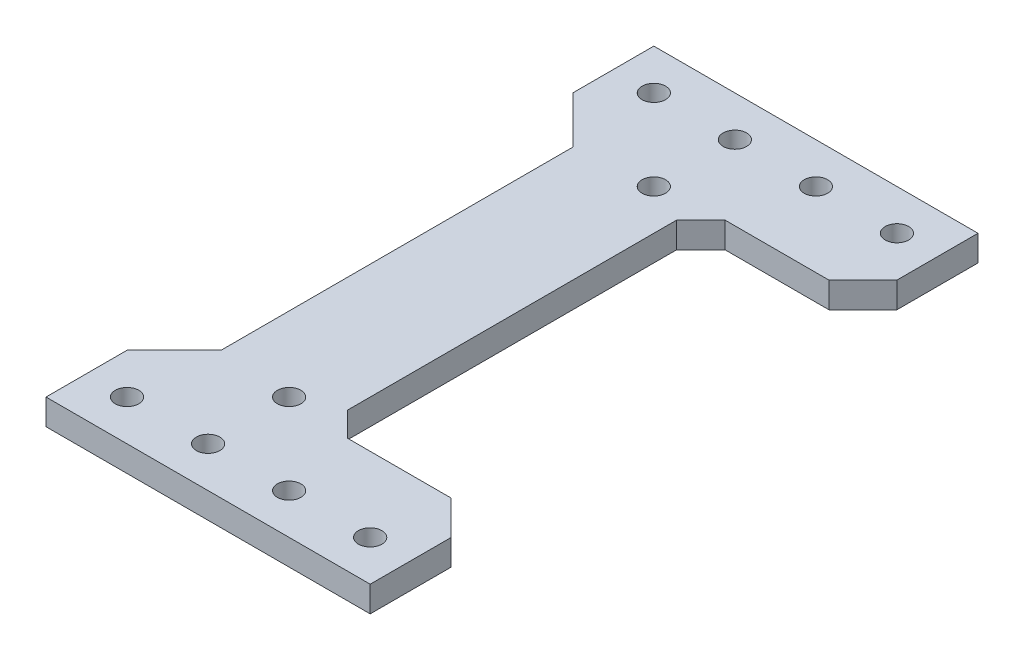
SolidWorks part; units mm, degrees
ref_plane "Front Plane" through (0, 0, 0) normal (0, 0, 1) x (1, 0, 0)
ref_plane "Top Plane" through (0, 0, 0) normal (0, 1, 0) x (1, 0, 0)
ref_plane "Right Plane" through (0, 0, 0) normal (1, 0, 0) x (0, 0, -1)
sketch "Sketch1" plane through (0, 0, 0) normal (0, 1, 0) x (1, 0, 0)
  line L0 (5, 23.3) -> (25, 23.3)
  line L1 (5, 0) -> (-9.2, 0)
  line L2 (5, 0) -> (5, 23.3)
  line L3 (-20, 32.5) -> (25, 32.5) construction
  line L4 (-9.2, 0) -> (-9.2, 21.7)
  line L5 (-15, 37.5) -> (25, 37.5)
  line L6 (-15, 37.5) -> (-15, 27.5)
  line L7 (-15, 27.5) -> (-9.2, 21.7)
  line L8 (25, 37.5) -> (25, 23.3)
  circle A0 centre (0, 22.5) radius 1.45
  circle A1 centre (-10, 32.5) radius 1.45
  circle A2 centre (20, 32.5) radius 1.45
  circle A3 centre (0, 32.5) radius 1.45
  circle A4 centre (10, 32.5) radius 1.45
  dimension "D4" = 2.9
  dimension "D1" = 37.5
  dimension "D2" = 10
  dimension "D3" = 14.2
  dimension "D5" = 20
  dimension "D6" = 10
  dimension "D7" = 5
  dimension "D8" = 10
  dimension "D9" = 5
  dimension "D10" = 5
  dimension "D11" = 32.5
  dimension "D12" = 45
  dimension "D13" = 14.2
  dimension "D14" = 10
extrude "Boss-Extrude1" add sketch "Sketch1" along normal blind 3.175
mirror "Mirror1" about plane through (5, 3.175, 0) normal (0, 0, -1) of "Boss-Extrude1"
chamfer "Chamfer1" distance 4.2 angle 45 2 edges at (25, 1.5875, 23.3) (25, 1.5875, -23.3)
chamfer "Chamfer2" distance 3 angle 45 2 edges at (5, 1.5875, -23.3) (5, 1.5875, 23.3)
sketch "Sketch2" [suppressed] plane through (0, 3.175, 0) normal (0, 1, 0) x (1, 0, 0)
  line L0 (25, 37.5) -> (-15, 37.5) construction
  line L1 (-5, 37.5) -> (-15, 37.5)
  line L2 (-5, 37.5) -> (-5, -37.5)
  line L3 (-5, -37.5) -> (-15, -37.5)
  line L4 (-15, 37.5) -> (-15, -37.5)
  dimension "D1" = 5
extrude "Cut-Extrude1" [suppressed] cut sketch "Sketch2" against normal through all
sketch "Sketch3" [suppressed] plane through (0, 3.175, 0) normal (0, 1, 0) x (1, 0, 0)
  line L0 (25, 37.5) -> (-9.2, 37.5) construction
  line L1 (-9.2, -33.7093) -> (-6.1445, -33.7093)
  line L2 (-9.2, -33.7093) -> (-9.2, 37.5)
  line L3 (-9.2, 37.5) -> (-6.1445, 37.5)
  line L4 (-6.1445, -33.7093) -> (-6.1445, 37.5)
extrude "Boss-Extrude2" [suppressed] add sketch "Sketch3" against normal up to surface (3.175 mm away)
